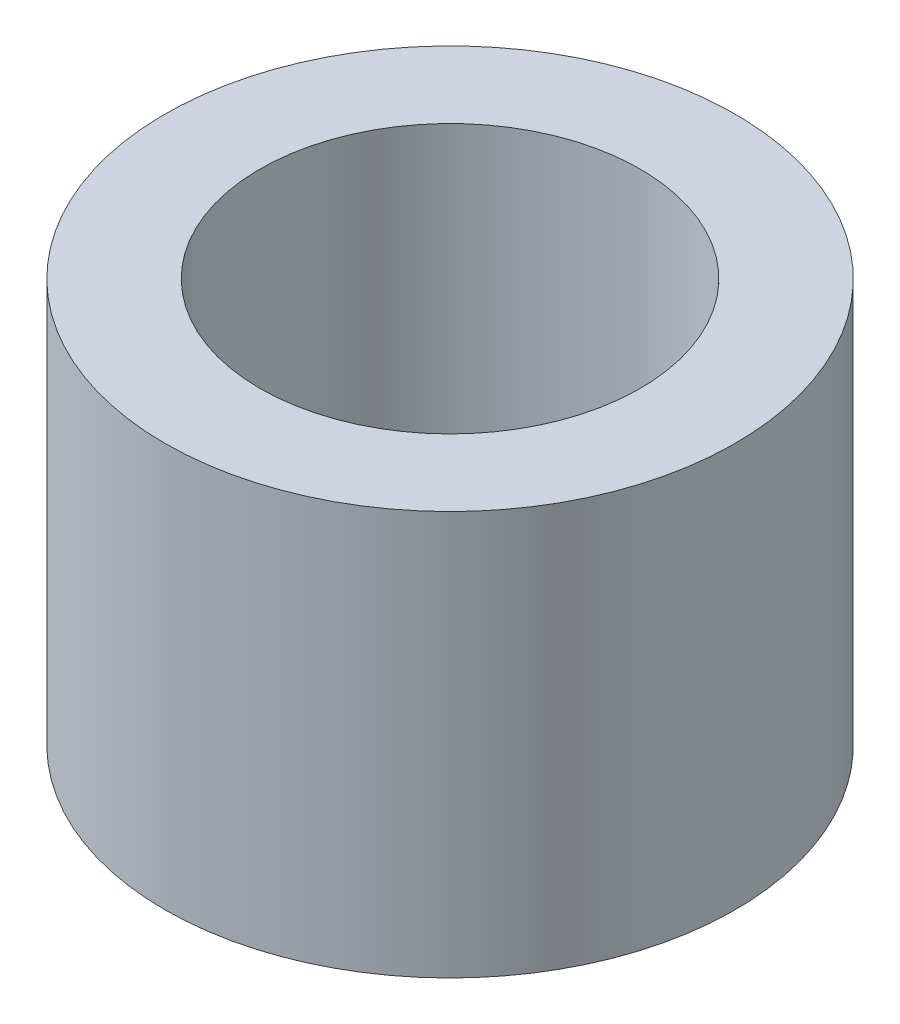
SolidWorks part; units mm, degrees
ref_plane "Front Plane" through (0, 0, 0) normal (0, 0, 1) x (1, 0, 0)
ref_plane "Top Plane" through (0, 0, 0) normal (0, 1, 0) x (1, 0, 0)
ref_plane "Right Plane" through (0, 0, 0) normal (1, 0, 0) x (0, 0, -1)
sketch "Sketch1" plane through (0, 0, 0) normal (0, 1, 0) x (1, 0, 0)
  circle A0 centre (0, 0) radius 4
  circle A1 centre (0, 0) radius 6
  dimension "D1" = 12
  dimension "D2" = 8
extrude "Boss-Extrude1" add sketch "Sketch1" along normal blind 8.5
